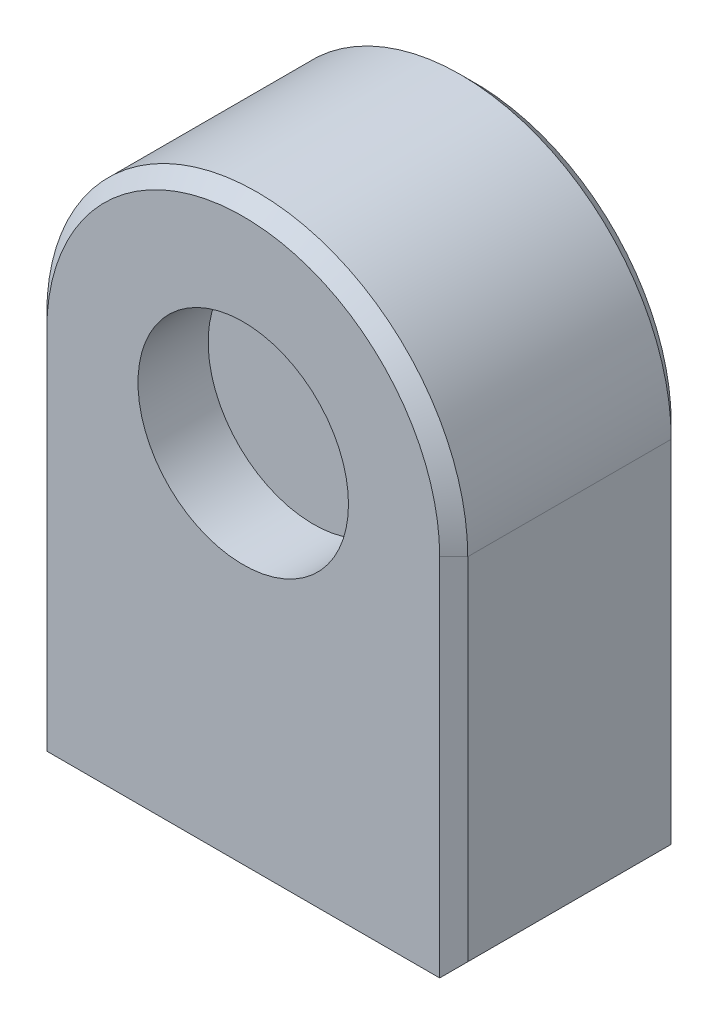
SolidWorks part; units mm, degrees
ref_plane "Front" through (0, 0, 0) normal (0, 0, 1) x (1, 0, 0)
ref_plane "Top" through (0, 0, 0) normal (0, 1, 0) x (1, 0, 0)
ref_plane "Right" through (0, 0, 0) normal (1, 0, 0) x (0, 0, -1)
sketch "草圖1" plane through (0, 0, 0) normal (0, 0, 1) x (1, 0, 0)
  line L0 (-15, 0) -> (15, 0) construction
  line L2 (-15, 0) -> (-15, -26)
  line L3 (-15, -26) -> (15, -26)
  line L4 (15, 0) -> (15, -26)
  arc A0 (-15, 0) -> (15, 0) centre (0, 0) cw
  dimension "D1" = 15
  dimension "D2" = 26
  dimension "D3" = 30
extrude "填料-伸長1" add sketch "草圖1" along normal blind 16.5
chamfer "導角1" distance 1 angle 45 8 edges at (15, -13, 16.5) (15, -13, 0) (0, 15, 16.5) (0, 15, 0) (-15, -13, 16.5) (-15, -13, 0) (-15, -26, 8.25) (15, -26, 8.25)
sketch "草圖2" plane through (0, 0, 16.5) normal (0, 0, 1) x (1, 0, 0)
  circle A0 centre (0, 0) radius 7.5
  dimension "D1" = 15
extrude "除料-伸長1" cut sketch "草圖2" against normal blind 5
